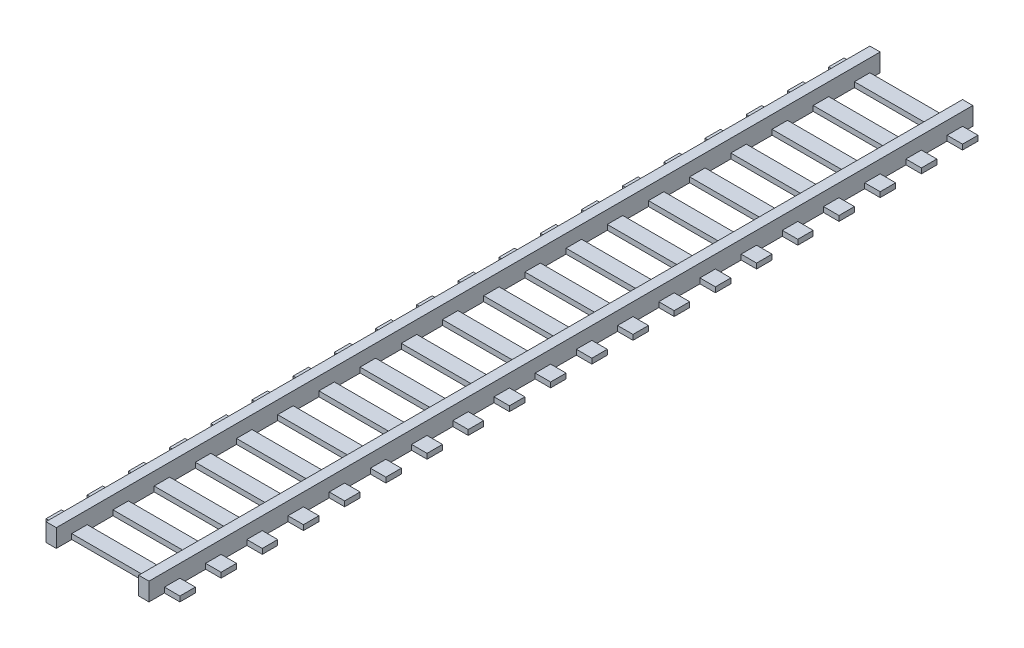
SolidWorks part; units mm, degrees
ref_plane "Front Plane" through (0, 0, 0) normal (0, 0, 1) x (1, 0, 0)
ref_plane "Top Plane" through (0, 0, 0) normal (0, 1, 0) x (1, 0, 0)
ref_plane "Right Plane" through (0, 0, 0) normal (1, 0, 0) x (0, 0, -1)
sketch "Sketch1" plane through (0, 0, 0) normal (0, 1, 0) x (1, 0, 0)
  line L1 (-43.6876, 71.25) -> (-42.6876, 71.25)
  line L2 (-43.6876, 71.25) -> (-43.6876, -88.75)
  line L3 (-43.6876, -88.75) -> (-42.6876, -88.75)
  line L4 (-42.6876, 71.25) -> (-42.6876, -88.75)
  line L5 (-26.6876, 71.25) -> (-25.6876, 71.25)
  line L6 (-26.6876, 71.25) -> (-26.6876, -88.75)
  line L7 (-26.6876, -88.75) -> (-25.6876, -88.75)
  line L8 (-25.6876, 71.25) -> (-25.6876, -88.75)
  dimension "D1" = 160
  dimension "D2" = 1
  dimension "D3" = 1
  dimension "D4" = 16
extrude "Boss-Extrude1" add sketch "Sketch1" along normal blind 3
sketch "Sketch2" plane through (0, 0, 0) normal (0, -1, 0) x (1, 0, 0)
  line L0 (-43.6876, -71.25) -> (-43.6876, 88.75) construction
  line L1 (-43.6876, -71.25) -> (-43.6876, 88.75)
  line L2 (-44.6876, -71.25) -> (-44.6876, 88.75)
  line L3 (-43.6876, -71.25) -> (-44.6876, -71.25)
  line L4 (-43.6876, 88.75) -> (-44.6876, 88.75)
  line L5 (-25.6876, 88.75) -> (-25.6876, -71.25) construction
  line L6 (-25.6876, 88.75) -> (-25.6876, -71.25)
  line L7 (-24.6876, 88.75) -> (-24.6876, -71.25)
  line L8 (-25.6876, 88.75) -> (-24.6876, 88.75)
  line L9 (-25.6876, -71.25) -> (-24.6876, -71.25)
  dimension "D1" = 1
  dimension "D2" = 1
extrude "Boss-Extrude2" add sketch "Sketch2" against normal up to surface (3 mm away) up to face at (-43.1876, 3, 8.75)
sketch "Sketch3" plane through (0, 0, 0) normal (0, -1, 0) x (1, 0, 0)
  line L0 (-44.6876, 88.75) -> (-44.6876, -71.25) construction
  line L1 (-47.6876, 85.75) -> (-21.6876, 85.75)
  line L2 (-47.6876, 85.75) -> (-47.6876, 82.75)
  line L3 (-47.6876, 82.75) -> (-21.6876, 82.75)
  line L4 (-21.6876, 85.75) -> (-21.6876, 82.75)
  line L5 (-24.6876, -71.25) -> (-24.6876, 88.75) construction
  line L6 (-47.6876, 77.75) -> (-47.6876, 74.75)
  line L7 (-47.6876, 77.75) -> (-21.6876, 77.75)
  line L8 (-21.6876, 77.75) -> (-21.6876, 74.75)
  line L9 (-47.6876, 74.75) -> (-21.6876, 74.75)
  line L10 (-47.6876, 69.75) -> (-47.6876, 66.75)
  line L11 (-47.6876, 69.75) -> (-21.6876, 69.75)
  line L12 (-21.6876, 69.75) -> (-21.6876, 66.75)
  line L13 (-47.6876, 66.75) -> (-21.6876, 66.75)
  line L14 (-47.6876, 61.75) -> (-47.6876, 58.75)
  line L15 (-47.6876, 61.75) -> (-21.6876, 61.75)
  line L16 (-21.6876, 61.75) -> (-21.6876, 58.75)
  line L17 (-47.6876, 58.75) -> (-21.6876, 58.75)
  line L18 (-47.6876, 53.75) -> (-47.6876, 50.75)
  line L19 (-47.6876, 53.75) -> (-21.6876, 53.75)
  line L20 (-21.6876, 53.75) -> (-21.6876, 50.75)
  line L21 (-47.6876, 50.75) -> (-21.6876, 50.75)
  line L22 (-47.6876, 45.75) -> (-47.6876, 42.75)
  line L23 (-47.6876, 45.75) -> (-21.6876, 45.75)
  line L24 (-21.6876, 45.75) -> (-21.6876, 42.75)
  line L25 (-47.6876, 42.75) -> (-21.6876, 42.75)
  line L26 (-47.6876, 37.75) -> (-47.6876, 34.75)
  line L27 (-47.6876, 37.75) -> (-21.6876, 37.75)
  line L28 (-21.6876, 37.75) -> (-21.6876, 34.75)
  line L29 (-47.6876, 34.75) -> (-21.6876, 34.75)
  line L30 (-47.6876, 29.75) -> (-47.6876, 26.75)
  line L31 (-47.6876, 29.75) -> (-21.6876, 29.75)
  line L32 (-21.6876, 29.75) -> (-21.6876, 26.75)
  line L33 (-47.6876, 26.75) -> (-21.6876, 26.75)
  line L34 (-47.6876, 21.75) -> (-47.6876, 18.75)
  line L35 (-47.6876, 21.75) -> (-21.6876, 21.75)
  line L36 (-21.6876, 21.75) -> (-21.6876, 18.75)
  line L37 (-47.6876, 18.75) -> (-21.6876, 18.75)
  line L38 (-47.6876, 13.75) -> (-47.6876, 10.75)
  line L39 (-47.6876, 13.75) -> (-21.6876, 13.75)
  line L40 (-21.6876, 13.75) -> (-21.6876, 10.75)
  line L41 (-47.6876, 10.75) -> (-21.6876, 10.75)
  line L42 (-47.6876, 5.75) -> (-47.6876, 2.75)
  line L43 (-47.6876, 5.75) -> (-21.6876, 5.75)
  line L44 (-21.6876, 5.75) -> (-21.6876, 2.75)
  line L45 (-47.6876, 2.75) -> (-21.6876, 2.75)
  line L46 (-47.6876, -2.25) -> (-47.6876, -5.25)
  line L47 (-47.6876, -2.25) -> (-21.6876, -2.25)
  line L48 (-21.6876, -2.25) -> (-21.6876, -5.25)
  line L49 (-47.6876, -5.25) -> (-21.6876, -5.25)
  line L50 (-47.6876, -10.25) -> (-47.6876, -13.25)
  line L51 (-47.6876, -10.25) -> (-21.6876, -10.25)
  line L52 (-21.6876, -10.25) -> (-21.6876, -13.25)
  line L53 (-47.6876, -13.25) -> (-21.6876, -13.25)
  line L54 (-47.6876, -18.25) -> (-47.6876, -21.25)
  line L55 (-47.6876, -18.25) -> (-21.6876, -18.25)
  line L56 (-21.6876, -18.25) -> (-21.6876, -21.25)
  line L57 (-47.6876, -21.25) -> (-21.6876, -21.25)
  line L58 (-47.6876, -26.25) -> (-47.6876, -29.25)
  line L59 (-47.6876, -26.25) -> (-21.6876, -26.25)
  line L60 (-21.6876, -26.25) -> (-21.6876, -29.25)
  line L61 (-47.6876, -29.25) -> (-21.6876, -29.25)
  line L62 (-47.6876, -34.25) -> (-47.6876, -37.25)
  line L63 (-47.6876, -34.25) -> (-21.6876, -34.25)
  line L64 (-21.6876, -34.25) -> (-21.6876, -37.25)
  line L65 (-47.6876, -37.25) -> (-21.6876, -37.25)
  line L66 (-47.6876, -42.25) -> (-47.6876, -45.25)
  line L67 (-47.6876, -42.25) -> (-21.6876, -42.25)
  line L68 (-21.6876, -42.25) -> (-21.6876, -45.25)
  line L69 (-47.6876, -45.25) -> (-21.6876, -45.25)
  line L70 (-47.6876, -50.25) -> (-47.6876, -53.25)
  line L71 (-47.6876, -50.25) -> (-21.6876, -50.25)
  line L72 (-21.6876, -50.25) -> (-21.6876, -53.25)
  line L73 (-47.6876, -53.25) -> (-21.6876, -53.25)
  line L74 (-47.6876, -58.25) -> (-47.6876, -61.25)
  line L75 (-47.6876, -58.25) -> (-21.6876, -58.25)
  line L76 (-21.6876, -58.25) -> (-21.6876, -61.25)
  line L77 (-47.6876, -61.25) -> (-21.6876, -61.25)
  line L78 (-47.6876, -66.25) -> (-47.6876, -69.25)
  line L79 (-47.6876, -66.25) -> (-21.6876, -66.25)
  line L80 (-21.6876, -66.25) -> (-21.6876, -69.25)
  line L81 (-47.6876, -69.25) -> (-21.6876, -69.25)
  dimension "D1" = 3
  dimension "D2" = 3
  dimension "D3" = 3
  dimension "D4" = 3
  dimension "D6" = 3
  dimension "D5" = 20
extrude "Boss-Extrude3" add sketch "Sketch3" against normal blind 1
sketch "Sketch5" plane through (0, 3, 0) normal (0, 1, 0) x (1, 0, 0)
  line L4 (-42.6876, 71.25) -> (-44.6876, 71.25)
  line L5 (-44.6876, 71.25) -> (-44.6876, -88.75)
  line L6 (-44.6876, -88.75) -> (-42.6876, -88.75)
  line L7 (-42.6876, -88.75) -> (-42.6876, 71.25)
  line L8 (-42.6876, 71.25) -> (-44.6876, 71.25)
  line L9 (-44.6876, 71.25) -> (-44.6876, -88.75)
  line L10 (-44.6876, -88.75) -> (-42.6876, -88.75)
  line L11 (-42.6876, -88.75) -> (-42.6876, 71.25)
  line L12 (-26.6876, 71.25) -> (-26.6876, -88.75)
  line L13 (-26.6876, -88.75) -> (-24.6876, -88.75)
  line L14 (-24.6876, -88.75) -> (-24.6876, 71.25)
  line L15 (-24.6876, 71.25) -> (-26.6876, 71.25)
  line L16 (-26.6876, 71.25) -> (-26.6876, -88.75)
  line L17 (-26.6876, -88.75) -> (-24.6876, -88.75)
  line L18 (-24.6876, -88.75) -> (-24.6876, 71.25)
  line L19 (-24.6876, 71.25) -> (-26.6876, 71.25)
  dimension "D1" = 0
  dimension "D2" = 0
extrude "Boss-Extrude4" add sketch "Sketch5" along normal blind 0.5
sketch "Sketch6" plane through (0, 0, -71.25) normal (0, 0, -1) x (-1, 0, 0)
  line L0 (44.6876, 3.5) -> (44.6876, 0) construction
  line L1 (44.6876, 3.5) -> (44.6876, 0)
  dimension "D1" = 3.5
